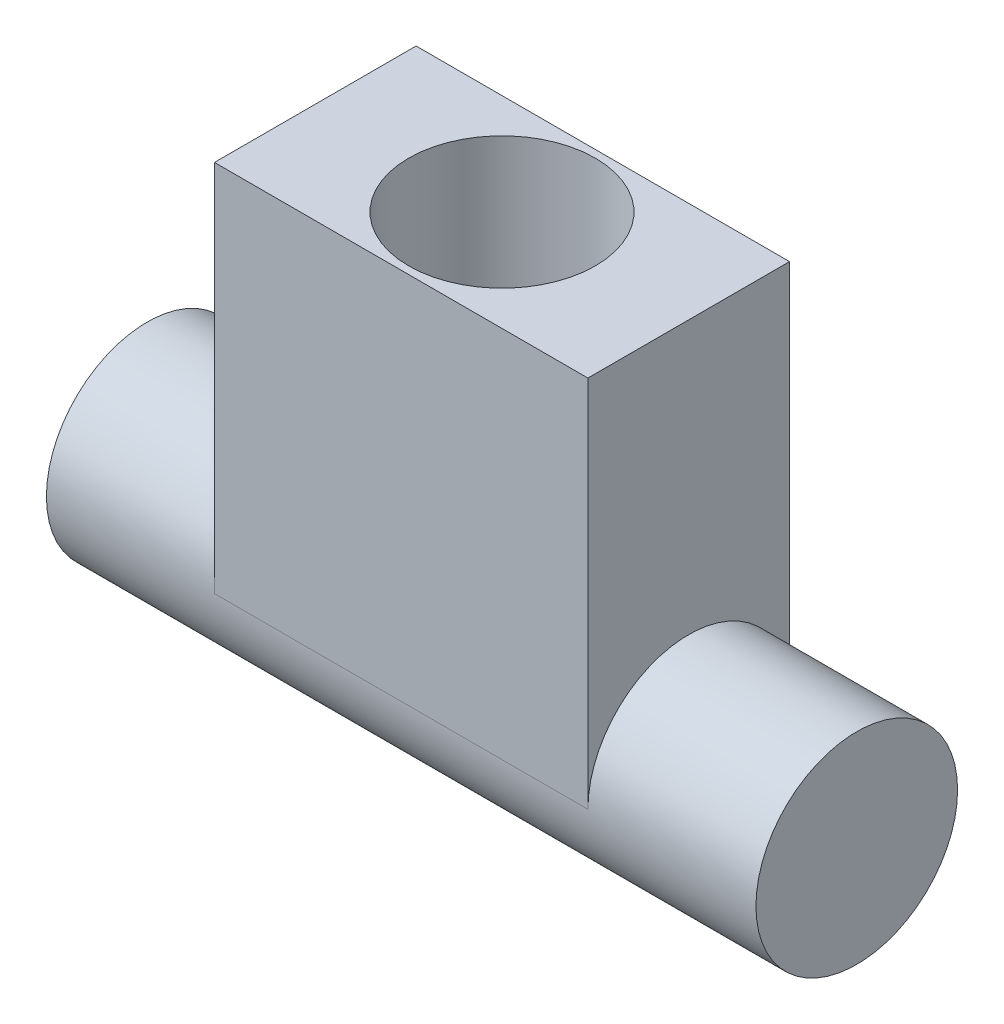
SolidWorks part; units mm, degrees
ref_plane "Front Plane" through (0, 0, 0) normal (0, 0, 1) x (1, 0, 0)
ref_plane "Top Plane" through (0, 0, 0) normal (0, 1, 0) x (1, 0, 0)
ref_plane "Right Plane" through (0, 0, 0) normal (1, 0, 0) x (0, 0, -1)
sketch "Sketch1" plane through (0, 0, 0) normal (1, 0, 0) x (0, 0, -1)
  circle A0 centre (0, 0) radius 2.7
  dimension "D1" = 5.4
extrude "Boss-Extrude1" add sketch "Sketch1" along normal blind 19
sketch "Sketch2" plane through (0, 0, 0) normal (0, 1, 0) x (1, 0, 0)
  line L0 (0, 0) -> (19, 0) construction
  line L1 (19, -2.7) -> (19, 2.7) construction
  line L2 (0, -2.7) -> (19, -2.7) construction
  line L3 (4.5, 2.7) -> (14.5, 2.7)
  line L4 (4.5, 2.7) -> (4.5, -2.7)
  line L5 (4.5, -2.7) -> (14.5, -2.7)
  line L6 (14.5, 2.7) -> (14.5, -2.7)
  line L7 (4.5, 2.7) -> (14.5, -2.7) construction
  line L8 (4.5, -2.7) -> (14.5, 2.7) construction
  point P5 (9.5, 0)
  dimension "D1" = 10
extrude "Boss-Extrude2" add sketch "Sketch2" along normal blind 10
sketch "Sketch3" plane through (0, 10, 0) normal (0, 1, 0) x (1, 0, 0)
  line L0 (4.5, 0) -> (14.5, 0) construction
  line L1 (4.5, 2.7) -> (4.5, -2.7) construction
  line L2 (14.5, -2.7) -> (14.5, 2.7) construction
  circle A0 centre (9.5, 0) radius 2.5
  dimension "D1" = 5
extrude "Cut-Extrude1" cut sketch "Sketch3" against normal blind 5
